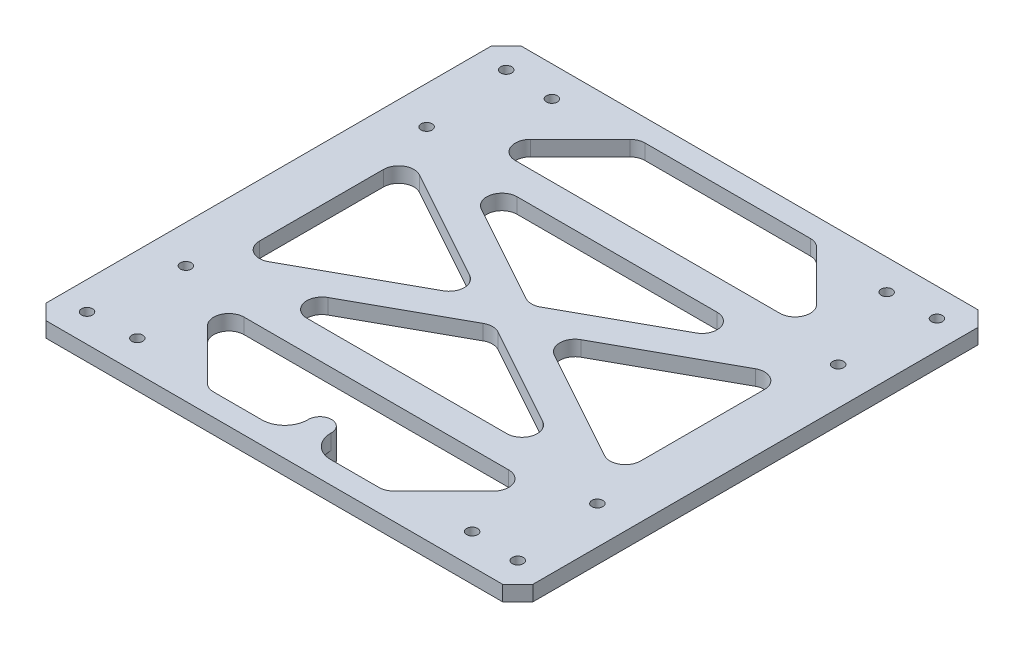
SolidWorks part; units mm, degrees
ref_plane "Front Plane" through (0, 0, 0) normal (0, 0, 1) x (1, 0, 0)
ref_plane "Top Plane" through (0, 0, 0) normal (0, 1, 0) x (1, 0, 0)
ref_plane "Right Plane" through (0, 0, 0) normal (1, 0, 0) x (0, 0, -1)
sketch "Sketch1" plane through (0, 0, 0) normal (0, 1, 0) x (1, 0, 0)
  line L0 (0, 192.024) -> (6.35, 198.374)
  line L1 (6.35, 0) -> (196.85, 0)
  line L2 (0, 6.35) -> (0, 192.024)
  line L3 (6.35, 198.374) -> (196.85, 198.374)
  line L4 (203.2, 6.35) -> (203.2, 192.024)
  line L5 (196.85, 198.374) -> (203.2, 192.024)
  line L6 (196.85, 0) -> (203.2, 6.35)
  line L7 (0, 6.35) -> (6.35, 0)
  point P0 (0, 0)
  point P1 (203.2, 198.374)
  point P2 (0, 198.374)
  point P3 (203.2, 0)
  dimension "D1" = 198.374
  dimension "D2" = 203.2
extrude "Boss-Extrude1" add sketch "Sketch1" along normal blind 6.35
sketch "Sketch3" plane through (0, 6.35, 0) normal (0, 1, 0) x (1, 0, 0)
  line L0 (6.35, 0) -> (196.85, 0) construction
  line L1 (0, 192.024) -> (0, 6.35) construction
  line L2 (203.2, 6.35) -> (203.2, 192.024) construction
  line L3 (196.85, 198.374) -> (6.35, 198.374) construction
  circle A0 centre (11.7373, 11.7373) radius 2.286
  circle A1 centre (191.4627, 11.7373) radius 2.286
  circle A2 centre (191.4627, 186.6367) radius 2.286
  circle A3 centre (11.7373, 186.6367) radius 2.286
  dimension "D1" = 2
  dimension "D3" = 4.572
  dimension "D4" = 11.7373
  dimension "D5" = 11.7373
  dimension "D6" = 11.7373
  dimension "D7" = 11.7373
  dimension "D8" = 11.7373
  dimension "D2" = 2
extrude "Cut-Extrude2" cut sketch "Sketch3" against normal through all
sketch "Sketch4" plane through (0, 6.35, 0) normal (0, 1, 0) x (1, 0, 0)
  line L0 (0, 192.024) -> (0, 6.35) construction
  line L1 (15.748, 149.4155) -> (187.452, 149.4155) construction
  line L2 (15.748, 149.4155) -> (15.748, 48.9585) construction
  line L3 (15.748, 48.9585) -> (187.452, 48.9585) construction
  line L4 (187.452, 149.4155) -> (187.452, 48.9585) construction
  line L5 (196.85, 198.374) -> (6.35, 198.374) construction
  line L6 (12.573, 137.2602) -> (64.4907, 189.178)
  line L7 (138.7093, 189.178) -> (64.4907, 189.178)
  line L8 (138.7093, 189.178) -> (190.627, 137.2602)
  line L9 (190.627, 61.1138) -> (138.7093, 9.196)
  line L10 (190.627, 137.2602) -> (190.627, 61.1138)
  line L11 (138.7093, 9.196) -> (64.4907, 9.196)
  line L12 (64.4907, 9.196) -> (12.573, 61.1138)
  line L13 (12.573, 61.1138) -> (12.573, 137.2602)
  circle A0 centre (15.748, 149.4155) radius 2.286
  circle A1 centre (187.452, 149.4155) radius 2.286
  circle A2 centre (187.452, 48.9585) radius 2.286
  circle A3 centre (15.748, 48.9585) radius 2.286
  point P6 (0, 99.187)
  point P7 (15.748, 99.187)
  point P10 (101.6, 198.374)
  point P11 (101.6, 149.4155)
  dimension "D3" = 4.572
  dimension "D5" = 6.35
  dimension "D7" = 6.35
  dimension "D1" = 171.704
  dimension "D2" = 100.457
  dimension "D4" = 6.35
  dimension "D6" = 6.35
  dimension "D8" = 6.35
extrude "Cut-Extrude3" cut sketch "Sketch4" against normal through all
sketch "Sketch5" plane through (0, 6.35, 0) normal (0, 1, 0) x (1, 0, 0)
  line L0 (15.748, 48.9585) -> (187.452, 48.9585) construction
  line L1 (187.452, 48.9585) -> (187.452, 149.4155) construction
  line L2 (187.452, 149.4155) -> (15.748, 149.4155) construction
  line L3 (15.748, 149.4155) -> (15.748, 48.9585) construction
  line L4 (193.802, 155.7655) -> (9.398, 155.7655)
  line L5 (9.398, 155.7655) -> (9.398, 42.6085)
  line L6 (9.398, 42.6085) -> (193.802, 42.6085)
  line L7 (193.802, 42.6085) -> (193.802, 155.7655)
  line L8 (143.3139, 143.0655) -> (59.8861, 143.0655)
  line L9 (22.098, 125.0549) -> (22.098, 73.3191)
  line L10 (59.8861, 55.3085) -> (143.3139, 55.3085)
  line L11 (181.102, 73.3191) -> (181.102, 125.0549)
  line L12 (22.098, 55.3085) -> (181.102, 143.0655) construction
  line L13 (181.102, 55.3085) -> (22.098, 143.0655) construction
  line L14 (56.8177, 67.218) -> (98.5316, 90.2406)
  line L15 (171.6836, 67.7596) -> (124.8144, 93.6275)
  line L16 (31.5164, 67.7596) -> (78.3856, 93.6275)
  line L17 (146.3823, 67.218) -> (104.6684, 90.2406)
  line L18 (184.1704, 60.868) -> (25.1664, 148.625) construction
  line L19 (178.0336, 49.749) -> (19.0296, 137.506) construction
  line L20 (19.0296, 60.868) -> (178.0336, 148.625) construction
  line L21 (25.1664, 49.749) -> (184.1704, 137.506) construction
  line L22 (22.098, 55.3085) -> (181.102, 55.3085) construction
  line L23 (181.102, 55.3085) -> (181.102, 143.0655) construction
  line L24 (181.102, 143.0655) -> (22.098, 143.0655) construction
  line L25 (22.098, 143.0655) -> (22.098, 55.3085) construction
  line L26 (78.3856, 104.7465) -> (31.5164, 130.6144)
  line L27 (104.6684, 108.1334) -> (146.3823, 131.156)
  line L28 (124.8144, 104.7465) -> (171.6836, 130.6144)
  line L29 (98.5316, 108.1334) -> (56.8177, 131.156)
  circle A0 centre (187.452, 48.9585) radius 2.286 construction
  circle A1 centre (187.452, 149.4155) radius 2.286 construction
  circle A2 centre (15.748, 149.4155) radius 2.286 construction
  circle A3 centre (15.748, 48.9585) radius 2.286 construction
  circle A4 centre (187.452, 48.9585) radius 2.286
  circle A5 centre (187.452, 149.4155) radius 2.286
  circle A6 centre (15.748, 149.4155) radius 2.286
  circle A7 centre (15.748, 48.9585) radius 2.286
  arc A8 (56.8177, 131.156) -> (59.8861, 143.0655) centre (59.8861, 136.7155) cw
  arc A9 (146.3823, 131.156) -> (143.3139, 143.0655) centre (143.3139, 136.7155) ccw
  arc A10 (171.6836, 130.6144) -> (181.102, 125.0549) centre (174.752, 125.0549) cw
  arc A11 (124.8144, 104.7465) -> (124.8144, 93.6275) centre (127.8827, 99.187) ccw
  arc A12 (171.6836, 67.7596) -> (181.102, 73.3191) centre (174.752, 73.3191) ccw
  arc A13 (146.3823, 67.218) -> (143.3139, 55.3085) centre (143.3139, 61.6585) cw
  arc A14 (104.6684, 90.2406) -> (98.5316, 90.2406) centre (101.6, 84.6811) ccw
  arc A15 (78.3856, 104.7465) -> (78.3856, 93.6275) centre (75.3173, 99.187) cw
  arc A16 (31.5164, 130.6144) -> (22.098, 125.0549) centre (28.448, 125.0549) ccw
  arc A17 (31.5164, 67.7596) -> (22.098, 73.3191) centre (28.448, 73.3191) cw
  arc A18 (56.8177, 67.218) -> (59.8861, 55.3085) centre (59.8861, 61.6585) ccw
  arc A19 (98.5316, 108.1334) -> (104.6684, 108.1334) centre (101.6, 113.6929) ccw
  dimension "D5" = 6.35
  dimension "D6" = 6.35
  dimension "D1" = 6.35
  dimension "D3" = 6.35
  dimension "D2" = 6.35
  dimension "D4" = 6.35
extrude "Boss-Extrude2" add sketch "Sketch5" against normal up to surface (6.35 mm away) up to face at (187.452, 0, -147.1295)
fillet "Fillet1" radius 6.35 8 edges at (138.7093, 3.175, -189.178) (64.4907, 3.175, -189.178) (31.0783, 3.175, -155.7655) (172.1217, 3.175, -155.7655) (64.4907, 3.175, -9.196) (31.0783, 3.175, -42.6085) (138.7093, 3.175, -9.196) (172.1217, 3.175, -42.6085)
sketch "Sketch6" plane through (0, 6.35, 0) normal (0, 1, 0) x (1, 0, 0)
  line L0 (6.35, 0) -> (196.85, 0) construction
  line L1 (67.121, 9.196) -> (136.079, 9.196) construction
  line L2 (87.2528, 9.196) -> (115.9472, 9.196)
  circle A0 centre (101.6, 19.05) radius 2.286 construction
  arc A1 (106.4247, 18.9394) -> (96.7753, 18.9394) centre (101.6, 19.05) ccw
  arc A2 (87.2528, 9.196) -> (96.7753, 18.9394) centre (87.2528, 18.721) ccw
  arc A3 (106.4247, 18.9394) -> (115.9472, 9.196) centre (115.9472, 18.721) ccw
  point P7 (101.6, 0)
  dimension "D1" = 19.05
  dimension "D2" = 4.572
  dimension "D3" = 2.54
  dimension "D4" = 19.05
extrude "Boss-Extrude3" add sketch "Sketch6" against normal up to surface (6.35 mm away) up to face at (101.6, 0, -23.9206)
sketch "Sketch8" plane through (0, 0, 0) normal (0, 1, 0) x (1, 0, 0)
  circle A0 centre (101.6, 19.05) radius 4.826
  circle A1 centre (101.6, 19.05) radius 2.286
  arc A2 (106.4247, 18.9394) -> (96.7753, 18.9394) centre (101.6, 19.05) ccw construction
  dimension "D1" = 4.572
extrude "Boss-Extrude4" add sketch "Sketch8" against normal blind 6.35
sketch "Sketch9" plane through (0, 0, 0) normal (0, 1, 0) x (1, 0, 0)
  line L0 (79.6765, 112.0135) -> (123.5235, 86.3605) construction
  line L1 (123.5235, 112.0135) -> (79.6765, 86.3605) construction
  circle A0 centre (121.9669, 111.1029) radius 1.8034 construction
  circle A1 centre (81.2331, 111.1029) radius 1.8034 construction
  circle A2 centre (81.2331, 87.2711) radius 1.8034 construction
  circle A3 centre (121.9669, 87.2711) radius 1.8034 construction
  circle A4 centre (81.2331, 111.1029) radius 3.8354
  circle A5 centre (121.9669, 111.1029) radius 3.8354
  circle A6 centre (121.9669, 87.2711) radius 3.8354
  circle A7 centre (81.2331, 87.2711) radius 3.8354
  point P8 (101.6, 99.187)
  dimension "D1" = 3.6068
  dimension "D2" = 50.8
  dimension "D3" = 119.34
  dimension "D4" = 2.032
extrude "Cut-Extrude4" cut sketch "Sketch9" along normal offset from surface (3.81 mm away) 2.54 up to face at (101.6, 6.35, -20.7136)
sketch "Sketch11" plane through (0, 0, 0) normal (0, -1, 0) x (1, 0, 0)
  line L0 (0, -192.024) -> (0, -6.35) construction
  line L1 (6.35, 0) -> (196.85, 0) construction
  line L2 (196.85, -198.374) -> (6.35, -198.374) construction
  line L3 (203.2, -6.35) -> (203.2, -192.024) construction
  circle A0 centre (31.75, -12.7) radius 2.286
  circle A1 centre (171.45, -12.7) radius 2.286
  circle A2 centre (171.45, -185.674) radius 2.286
  circle A3 centre (31.75, -185.674) radius 2.286
  dimension "D1" = 4.572
  dimension "D6" = 12.7
  dimension "D7" = 31.75
  dimension "D8" = 31.75
  dimension "D2" = 31.75
  dimension "D3" = 12.7
  dimension "D4" = 2
  dimension "D5" = 2
extrude "Cut-Extrude6" cut sketch "Sketch11" against normal through all and the other way through all
sketch "Sketch12" plane through (0, 6.35, 0) normal (0, 1, 0) x (1, 0, 0)
  circle A0 centre (100.4131, 99.7822) radius 4.7625
extrude "Cut-Extrude7" cut sketch "Sketch12" against normal up to surface (6.35 mm away) up to face at (31.75, 0, -187.96)
sketch "Sketch16" plane through (0, 6.35, 0) normal (0, 1, 0) x (1, 0, 0)
  line L1 (94.0631, 93.4322) -> (106.7631, 93.4322)
  line L2 (94.0631, 93.4322) -> (94.0631, 106.1322)
  line L3 (94.0631, 106.1322) -> (106.7631, 106.1322)
  line L4 (106.7631, 93.4322) -> (106.7631, 106.1322)
  line L5 (94.0631, 93.4322) -> (106.7631, 106.1322) construction
  line L6 (94.0631, 106.1322) -> (106.7631, 93.4322) construction
  point P0 (100.4131, 99.7822)
  dimension "D1" = 12.7
  dimension "D2" = 12.7
extrude "Boss-Extrude6" add sketch "Sketch16" against normal blind 5.08
